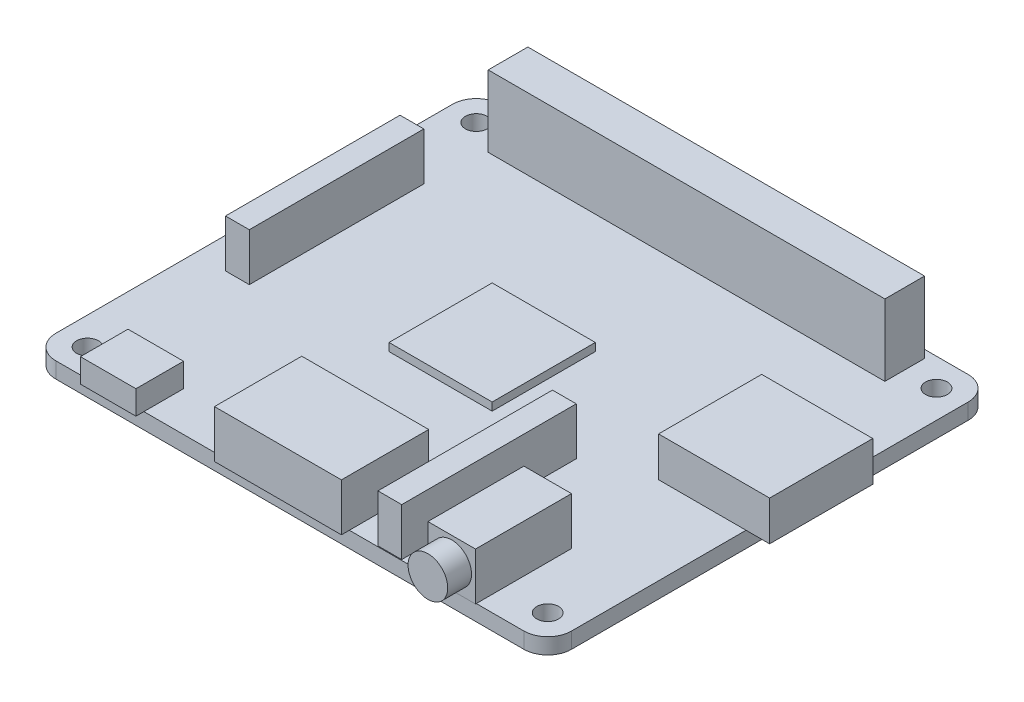
SolidWorks part; units mm, degrees
ref_plane "Front Plane" through (0, 0, 0) normal (0, 0, 1) x (1, 0, 0)
ref_plane "Top Plane" through (0, 0, 0) normal (0, 1, 0) x (1, 0, 0)
ref_plane "Right Plane" through (0, 0, 0) normal (1, 0, 0) x (0, 0, -1)
sketch "Sketch1" plane through (0, 0, 0) normal (0, 1, 0) x (1, 0, 0)
  line L1 (-32.5, 28) -> (32.5, 28)
  line L2 (-32.5, 28) -> (-32.5, -28)
  line L3 (-32.5, -28) -> (32.5, -28)
  line L4 (32.5, 28) -> (32.5, -28)
  line L5 (-32.5, 28) -> (32.5, -28) construction
  line L6 (-32.5, -28) -> (32.5, 28) construction
  point P0 (0, 0)
  dimension "D1" = 56
  dimension "D2" = 65
extrude "Boss-Extrude1" add sketch "Sketch1" along normal blind 2
sketch "Sketch2" plane through (0, 2, 0) normal (0, 1, 0) x (1, 0, 0)
  line L0 (-32.5, -28) -> (32.5, -28) construction
  line L1 (-32.5, 28) -> (-32.5, -28) construction
  line L2 (32.5, 28) -> (-32.5, 28) construction
  line L3 (32.5, -28) -> (32.5, 28) construction
  circle A0 centre (-29, -24.5) radius 1.375
  circle A1 centre (-29, 24.5) radius 1.375
  circle A2 centre (29, -24.5) radius 1.375
  circle A3 centre (29, 24.5) radius 1.375
  dimension "D1" = 2.75
  dimension "D3" = 3.5
  dimension "D4" = 2.75
  dimension "D7" = 2.75
  dimension "D8" = 2.75
  dimension "D2" = 3.5
  dimension "D5" = 3.5
  dimension "D6" = 3.5
  dimension "D9" = 3.5
  dimension "D10" = 3.5
  dimension "D11" = 3.5
  dimension "D12" = 3.5
extrude "Cut-Extrude1" cut sketch "Sketch2" against normal blind 2
fillet "Fillet1" radius 3 1 edges at (-32.5, 1, 28)
fillet "Fillet2" radius 3 1 edges at (32.5, 1, 28)
fillet "Fillet3" radius 3 1 edges at (32.5, 1, -28)
fillet "Fillet4" radius 3 1 edges at (-32.5, 1, -28)
sketch "Sketch3" plane through (0, 2, 0) normal (0, 1, 0) x (1, 0, 0)
  line L0 (29.5, 28) -> (-29.5, 28) construction
  line L1 (-25, 27) -> (25, 27)
  line L2 (-25, 27) -> (-25, 22)
  line L3 (-25, 22) -> (25, 22)
  line L4 (25, 27) -> (25, 22)
  line L5 (-25, 27) -> (25, 22) construction
  line L6 (-25, 22) -> (25, 27) construction
  circle A0 centre (-29, 24.5) radius 1.375 construction
  point P0 (0, 24.5)
  dimension "D4" = 29
  dimension "D1" = 50
  dimension "D2" = 5
  dimension "D3" = 1
extrude "Boss-Extrude2" add sketch "Sketch3" along normal blind 9
sketch "Sketch4" plane through (0, 2, 0) normal (0, 1, 0) x (1, 0, 0)
  line L1 (-28.6117, 14.5) -> (-25.6117, 14.5)
  line L2 (-28.6117, 14.5) -> (-28.6117, -7.5)
  line L3 (-28.6117, -7.5) -> (-25.6117, -7.5)
  line L4 (-25.6117, 14.5) -> (-25.6117, -7.5)
  line L5 (-28.6117, 14.5) -> (-25.6117, -7.5) construction
  line L6 (-28.6117, -7.5) -> (-25.6117, 14.5) construction
  circle A0 centre (-29, -24.5) radius 1.375 construction
  point P0 (-27.1117, 3.5)
  dimension "D3" = 28
  dimension "D1" = 22
  dimension "D2" = 3
extrude "Boss-Extrude3" add sketch "Sketch4" along normal blind 6
sketch "Sketch5" plane through (0, 2, 0) normal (0, 1, 0) x (1, 0, 0)
  line L0 (29.5, 28) -> (-29.5, 28) construction
  line L1 (21.4699, 10) -> (35.4699, 10)
  line L2 (21.4699, 10) -> (21.4699, -3)
  line L3 (21.4699, -3) -> (35.4699, -3)
  line L4 (35.4699, 10) -> (35.4699, -3)
  line L5 (21.4699, 10) -> (35.4699, -3) construction
  line L6 (21.4699, -3) -> (35.4699, 10) construction
  point P0 (28.4699, 3.5)
  dimension "D1" = 14
  dimension "D2" = 13
  dimension "D3" = 18
extrude "Boss-Extrude4" add sketch "Sketch5" along normal blind 5
sketch "Sketch6" plane through (0, 2, 0) normal (0, 1, 0) x (1, 0, 0)
  line L0 (-32.5, 25) -> (-32.5, -25) construction
  line L1 (17.5, -16) -> (23.5, -16)
  line L2 (17.5, -16) -> (17.5, -28.1)
  line L3 (17.5, -28.1) -> (23.5, -28.1)
  line L4 (23.5, -16) -> (23.5, -28.1)
  line L5 (17.5, -16) -> (23.5, -28.1) construction
  line L6 (17.5, -28.1) -> (23.5, -16) construction
  line L7 (29.5, 28) -> (-29.5, 28) construction
  point P0 (20.5, -22.05)
  dimension "D1" = 6
  dimension "D2" = 12.1
  dimension "D3" = 53
  dimension "D4" = 44
extrude "Boss-Extrude5" add sketch "Sketch6" along normal blind 6
sketch "Sketch7" plane through (0, 0, 28.1) normal (0, 0, 1) x (1, 0, 0)
  line L0 (17.5, 8) -> (17.5, 2) construction
  line L1 (17.5, 8) -> (23.5, 8) construction
  circle A0 centre (20.5, 5) radius 2.5
  dimension "D3" = 5
  dimension "D1" = 3
  dimension "D2" = 3
extrude "Boss-Extrude6" add sketch "Sketch7" along normal blind 3
sketch "Sketch8" plane through (0, 2, 0) normal (0, 1, 0) x (1, 0, 0)
  line L0 (-29.5, -28) -> (17.5, -28) construction
  line L1 (11, -5.9) -> (14, -5.9)
  line L2 (11, -5.9) -> (11, -27.9)
  line L3 (11, -27.9) -> (14, -27.9)
  line L4 (14, -5.9) -> (14, -27.9)
  line L5 (11, -5.9) -> (14, -27.9) construction
  line L6 (11, -27.9) -> (14, -5.9) construction
  line L7 (-32.5, 25) -> (-32.5, -25) construction
  point P0 (12.5, -16.9)
  dimension "D1" = 22
  dimension "D2" = 3
  dimension "D3" = 0.1
  dimension "D4" = 45
extrude "Boss-Extrude7" add sketch "Sketch8" along normal blind 6
sketch "Sketch9" plane through (0, 2, 0) normal (0, 1, 0) x (1, 0, 0)
  line L0 (-32.5, 25) -> (-32.5, -25) construction
  line L1 (-8.5, -18) -> (7.5, -18)
  line L2 (-8.5, -18) -> (-8.5, -29)
  line L3 (-8.5, -29) -> (7.5, -29)
  line L4 (7.5, -18) -> (7.5, -29)
  line L5 (-8.5, -18) -> (7.5, -29) construction
  line L6 (-8.5, -29) -> (7.5, -18) construction
  line L7 (29.5, 28) -> (-29.5, 28) construction
  point P0 (-0.5, -23.5)
  dimension "D1" = 16
  dimension "D2" = 11
  dimension "D3" = 32
  dimension "D4" = 46
extrude "Boss-Extrude8" add sketch "Sketch9" along normal blind 6
sketch "Sketch10" plane through (0, 2, 0) normal (0, 1, 0) x (1, 0, 0)
  line L0 (-32.5, 25) -> (-32.5, -25) construction
  line L1 (-25.4, -23) -> (-18.4, -23)
  line L2 (-25.4, -23) -> (-25.4, -29)
  line L3 (-25.4, -29) -> (-18.4, -29)
  line L4 (-18.4, -23) -> (-18.4, -29)
  line L5 (-25.4, -23) -> (-18.4, -29) construction
  line L6 (-25.4, -29) -> (-18.4, -23) construction
  line L7 (29.5, 28) -> (-29.5, 28) construction
  point P0 (-21.9, -26)
  dimension "D1" = 7
  dimension "D2" = 6
  dimension "D3" = 10.6
  dimension "D4" = 51
extrude "Boss-Extrude9" add sketch "Sketch10" along normal blind 3
sketch "Sketch11" plane through (0, 0, 0) normal (0, -1, 0) x (1, 0, 0)
  line L0 (29.5, -28) -> (-29.5, -28) construction
  line L1 (-17.5, -8) -> (-34.5, -8)
  line L2 (-17.5, -8) -> (-17.5, 5)
  line L3 (-17.5, 5) -> (-34.5, 5)
  line L4 (-34.5, -8) -> (-34.5, 5)
  line L5 (-17.5, -8) -> (-34.5, 5) construction
  line L6 (-17.5, 5) -> (-34.5, -8) construction
  line L7 (32.5, 25) -> (32.5, -25) construction
  point P0 (-26, -1.5)
  dimension "D1" = 17
  dimension "D2" = 13
  dimension "D3" = 20
  dimension "D4" = 50
extrude "Boss-Extrude10" add sketch "Sketch11" along normal blind 2
sketch "Sketch12" plane through (0, 2, 0) normal (0, 1, 0) x (1, 0, 0)
  line L0 (29.5, 28) -> (-29.5, 28) construction
  line L1 (-9.5, 7) -> (3.5, 7)
  line L2 (-9.5, 7) -> (-9.5, -6)
  line L3 (-9.5, -6) -> (3.5, -6)
  line L4 (3.5, 7) -> (3.5, -6)
  line L5 (-9.5, 7) -> (3.5, -6) construction
  line L6 (-9.5, -6) -> (3.5, 7) construction
  line L7 (-32.5, 25) -> (-32.5, -25) construction
  point P0 (-3, 0.5)
  dimension "D1" = 13
  dimension "D2" = 13
  dimension "D3" = 21
  dimension "D4" = 23
extrude "Boss-Extrude11" add sketch "Sketch12" along normal blind 1
